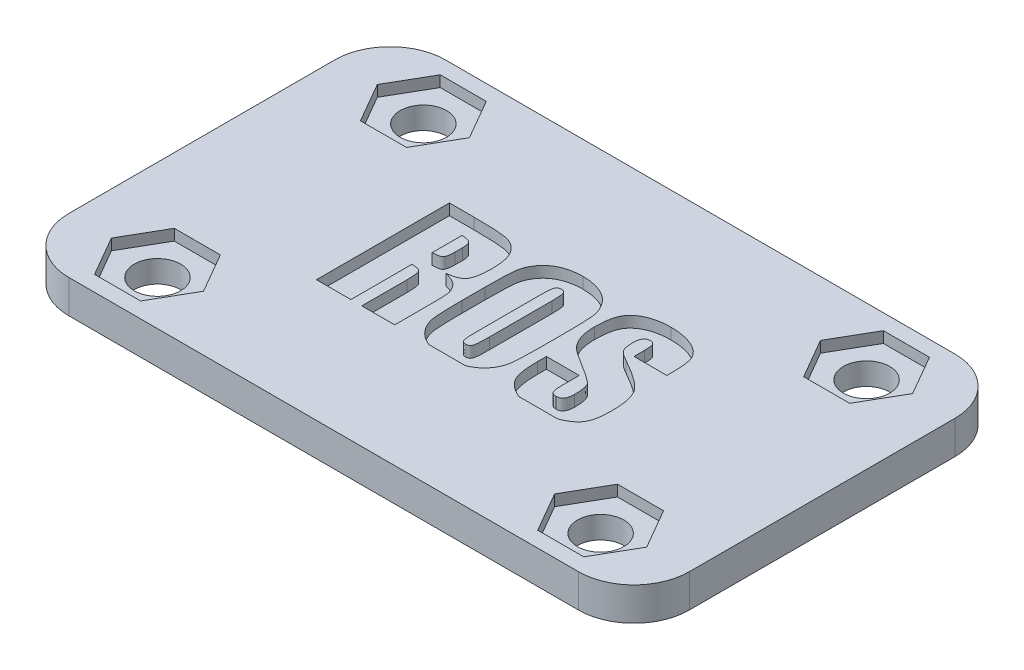
SolidWorks part; units mm, degrees
ref_plane "Front Plane" through (0, 0, 0) normal (0, 0, 1) x (1, 0, 0)
ref_plane "Top Plane" through (0, 0, 0) normal (0, 1, 0) x (1, 0, 0)
ref_plane "Right Plane" through (0, 0, 0) normal (1, 0, 0) x (0, 0, -1)
sketch "Sketch1" plane through (0, 0, 0) normal (0, 1, 0) x (1, 0, 0)
  line L1 (-28, 17) -> (28, 17)
  line L2 (-28, 17) -> (-28, -17)
  line L3 (-28, -17) -> (28, -17)
  line L4 (28, 17) -> (28, -17)
  line L5 (-28, 17) -> (28, -17) construction
  line L6 (-28, -17) -> (28, 17) construction
  point P0 (0, 0)
  dimension "D1" = 34
  dimension "D2" = 56
extrude "Boss-Extrude1" add sketch "Sketch1" along normal blind 3
sketch "Sketch2" plane through (0, 3, 0) normal (0, 1, 0) x (1, 0, 0)
  circle A0 centre (-20, 12) radius 2.09
  circle A1 centre (-20, -12) radius 2.09
  dimension "D1" = 4.18
  dimension "D2" = 24
  dimension "D3" = 12
  dimension "D4" = 20
extrude "Cut-Extrude1" cut sketch "Sketch2" against normal through all
mirror "Mirror1" about plane through (0, 0, 0) normal (1, 0, 0) of "Cut-Extrude1"
fillet "Fillet1" radius 5 4 edges at (28, 1.5, -17) (28, 1.5, 17) (-28, 1.5, 17) (-28, 1.5, -17)
sketch "Sketch3" plane through (0, 3, 0) normal (0, 1, 0) x (1, 0, 0)
  line L1 (-15.8431, 12) -> (-17.9215, 15.6)
  line L2 (-17.9215, 15.6) -> (-22.0785, 15.6)
  line L3 (-22.0785, 15.6) -> (-24.1569, 12)
  line L4 (-24.1569, 12) -> (-22.0785, 8.4)
  line L5 (-22.0785, 8.4) -> (-17.9215, 8.4)
  line L6 (-17.9215, 8.4) -> (-15.8431, 12)
  line L7 (24.1569, 12) -> (22.0785, 15.6)
  line L8 (22.0785, 15.6) -> (17.9215, 15.6)
  line L9 (17.9215, 15.6) -> (15.8431, 12)
  line L10 (15.8431, 12) -> (17.9215, 8.4)
  line L11 (17.9215, 8.4) -> (22.0785, 8.4)
  line L12 (22.0785, 8.4) -> (24.1569, 12)
  line L13 (-23, -17) -> (23, -17) construction
  circle A0 centre (-20, 12) radius 3.6 construction
  circle A1 centre (20, 12) radius 3.6 construction
  circle A2 centre (-20, 12) radius 2.09 construction
  circle A3 centre (20, 12) radius 2.09 construction
  dimension "D1" = 7.2
extrude "Cut-Extrude2" cut sketch "Sketch3" against normal blind 1
mirror "Mirror2" about plane through (0, 0, 0) normal (0, 0, 1) of "Cut-Extrude2"
sketch "Sketch4" plane through (0, 3, 0) normal (0, 1, 0) x (1, 0, 0)
  line L0 (-17, -6) -> (17, -6)
  line L1 (-11.6471, 6) -> (-9.4103, 6)
  line L2 (-4.5882, -2.7949) -> (-4.5882, -6)
  line L3 (-4.5882, -6) -> (-7.5529, -6)
  line L4 (-7.5529, -6) -> (-7.5529, -1.9412)
  line L5 (-8.5412, -0.4941) -> (-8.5412, -6)
  line L6 (-8.5412, -6) -> (-11.6471, -6)
  line L7 (-11.6471, -6) -> (-11.6471, 6)
  line L8 (-8.5412, 4.0235) -> (-8.5412, 1.3412)
  line L9 (-7.5529, 2.4287) -> (-7.5529, 3.0926)
  line L10 (-3.4588, -1.0324) -> (-3.4588, 1.0324)
  line L11 (3.7412, 1.0324) -> (3.7412, -1.0324)
  line L12 (-0.3529, 2.9757) -> (-0.3529, -2.7397)
  line L13 (0.6353, -2.6493) -> (0.6353, 2.9757)
  line L14 (11.6471, 2.3294) -> (8.6824, 2.3294)
  line L15 (8.6824, 2.3294) -> (8.6824, 3.2779)
  line L16 (4.7294, -2.4287) -> (4.7294, -1.6235)
  line L17 (4.7294, -1.6235) -> (7.6941, -1.6235)
  line L18 (7.6941, -1.6235) -> (7.6941, -3.1787)
  line L19 (11.6471, 2.8125) -> (11.6471, 2.3294)
  spline S0 degree 3 poles (-9.4103, 6) (-9.0669, 6.0012) (-8.5749, 5.9955) (-7.9492, 5.9771) (-7.5475, 5.9606) (-7.1909, 5.9363) (-6.8797, 5.9081) (-6.6138, 5.8763) (-6.3865, 5.8368) (-6.1862, 5.7853) (-6.0014, 5.7178) (-5.8245, 5.6374) (-5.6576, 5.5369) (-5.502, 5.419) (-5.352, 5.2894) (-5.2155, 5.1388) (-5.0841, 4.9743) (-4.9654, 4.7866) (-4.865, 4.5736) (-4.7788, 4.3358) (-4.7089, 4.0722) (-4.6548, 3.7831) (-4.5993, 3.3474) (-4.5915, 3.0059) (-4.5882, 2.7706) knots 0 0 0 0 0.148881 0.213303 0.271377 0.323138 0.368276 0.406827 0.439217 0.468212 0.496346 0.524443 0.552325 0.580569 0.609028 0.638128 0.668547 0.700209 0.734143 0.770448 0.80973 0.852244 0.897872 1 1 1 1
  spline S1 degree 3 poles (-4.5882, 2.7706) (-4.5847, 2.5592) (-4.5991, 2.256) (-4.6321, 1.8709) (-4.6732, 1.6245) (-4.7199, 1.4058) (-4.7787, 1.2138) (-4.8506, 1.0509) (-4.9341, 0.9125) (-5.0352, 0.7962) (-5.1554, 0.6939) (-5.2985, 0.6065) (-5.4611, 0.5289) (-5.6443, 0.4631) (-5.9295, 0.3905) (-6.1567, 0.3569) (-6.3154, 0.3441) knots 0 0 0 0 0.18379 0.264137 0.336087 0.400976 0.458649 0.510492 0.555595 0.598692 0.64408 0.692369 0.744168 0.800637 0.861472 1 1 1 1
  spline S2 degree 3 poles (-6.3154, 0.3441) (-6.1721, 0.3049) (-5.9643, 0.2494) (-5.706, 0.1522) (-5.5411, 0.0744) (-5.3931, -0.0045) (-5.2653, -0.0902) (-5.1556, -0.181) (-5.0387, -0.3053) (-4.9212, -0.4619) (-4.8041, -0.6448) (-4.7194, -0.8218) (-4.6697, -0.9719) (-4.6478, -1.1078) (-4.6293, -1.2429) (-4.6181, -1.4146) (-4.6068, -1.622) (-4.5986, -1.8647) (-4.5883, -2.2595) (-4.5915, -2.5736) (-4.5882, -2.7949) knots 0 0 0 0 0.11023 0.159227 0.204341 0.24532 0.283418 0.318243 0.350629 0.40972 0.463107 0.511383 0.554826 0.57974 0.613275 0.655917 0.707227 0.767226 0.835926 1 1 1 1
  spline S3 degree 3 poles (-7.5529, -1.9412) (-7.5542, -1.7934) (-7.554, -1.5834) (-7.5737, -1.3189) (-7.5901, -1.1553) (-7.6124, -1.0148) (-7.6369, -0.8974) (-7.67, -0.8034) (-7.7079, -0.7287) (-7.7573, -0.6684) (-7.8245, -0.6234) (-7.9036, -0.5807) (-8.0005, -0.548) (-8.1132, -0.5251) (-8.2947, -0.5004) (-8.4396, -0.4949) (-8.5412, -0.4941) knots 0 0 0 0 0.208712 0.296135 0.374434 0.440653 0.497065 0.543362 0.580978 0.614872 0.652041 0.694298 0.741574 0.795735 0.856514 1 1 1 1
  spline S4 degree 3 poles (-8.5412, 1.3412) (-8.3851, 1.3403) (-8.1682, 1.3525) (-7.9124, 1.4151) (-7.791, 1.4674) (-7.718, 1.5343) (-7.6711, 1.6021) (-7.6355, 1.6922) (-7.6049, 1.8009) (-7.5815, 1.9295) (-7.5561, 2.1403) (-7.5563, 2.3097) (-7.5529, 2.4287) knots 0 0 0 0 0.26319 0.361521 0.442778 0.481273 0.526535 0.580255 0.643242 0.716208 0.799609 1 1 1 1
  spline S5 degree 3 poles (-7.5529, 3.0926) (-7.5545, 3.251) (-7.5655, 3.4729) (-7.66, 3.7254) (-7.7586, 3.8532) (-7.9007, 3.9314) (-8.1584, 4.0148) (-8.3828, 4.0205) (-8.5412, 4.0235) knots 0 0 0 0 0.296724 0.405999 0.497474 0.590179 0.702697 1 1 1 1
  spline S6 degree 3 poles (3.7412, -1.0324) (3.7385, -1.3125) (3.74, -1.7169) (3.7317, -2.2339) (3.7191, -2.5721) (3.71, -2.8766) (3.6939, -3.1487) (3.6767, -3.3877) (3.6517, -3.661) (3.6003, -3.9749) (3.4883, -4.3317) (3.3296, -4.6711) (3.1303, -4.9928) (2.887, -5.2876) (2.6016, -5.5477) (2.2768, -5.7719) (1.913, -5.9572) (1.5147, -6.1011) (0.926, -6.2488) (0.4589, -6.2785) (0.1412, -6.2824) knots 0 0 0 0 0.112809 0.162854 0.208179 0.249065 0.285542 0.317902 0.345566 0.396043 0.445676 0.495616 0.546553 0.597656 0.649001 0.701564 0.75612 0.812885 0.871769 1 1 1 1
  spline S7 degree 3 poles (0.1412, -6.2824) (-0.1648, -6.2831) (-0.6144, -6.2452) (-1.1897, -6.1149) (-1.5848, -5.9757) (-1.9508, -5.7992) (-2.2779, -5.5765) (-2.5736, -5.321) (-2.8223, -5.0216) (-3.0318, -4.6996) (-3.1943, -4.3589) (-3.3103, -4.0053) (-3.368, -3.6952) (-3.392, -3.4245) (-3.4096, -3.1854) (-3.4246, -2.9111) (-3.4383, -2.603) (-3.4461, -2.2596) (-3.4555, -1.7324) (-3.458, -1.3191) (-3.4588, -1.0324) knots 0 0 0 0 0.123179 0.180929 0.237119 0.291548 0.344027 0.396062 0.448383 0.50021 0.550408 0.599943 0.649656 0.677029 0.709392 0.746168 0.787661 0.833574 0.884513 1 1 1 1
  spline S8 degree 3 poles (-3.4588, 1.0324) (-3.4561, 1.3132) (-3.4578, 1.7177) (-3.4492, 2.2346) (-3.437, 2.5721) (-3.4266, 2.8773) (-3.4146, 3.1495) (-3.3962, 3.3884) (-3.3721, 3.6612) (-3.3171, 3.9747) (-3.206, 4.3317) (-3.0479, 4.6709) (-2.8464, 4.9909) (-2.6056, 5.2885) (-2.3171, 5.546) (-1.9944, 5.773) (-1.63, 5.9562) (-1.2327, 6.1053) (-0.6417, 6.2443) (-0.1769, 6.2856) (0.1412, 6.2824) knots 0 0 0 0 0.1131 0.162847 0.20817 0.249054 0.28581 0.317873 0.345536 0.396062 0.445693 0.495631 0.546315 0.597643 0.649205 0.701523 0.756077 0.812942 0.872041 1 1 1 1
  spline S9 degree 3 poles (0.1412, 6.2824) (0.4469, 6.2818) (0.8967, 6.2477) (1.4702, 6.1117) (1.8645, 5.9733) (2.2316, 5.7988) (2.5599, 5.5778) (2.8536, 5.3201) (3.1028, 5.0218) (3.3114, 4.6989) (3.4772, 4.3595) (3.5927, 4.0046) (3.6506, 3.6938) (3.6735, 3.4229) (3.6959, 3.1849) (3.7057, 2.911) (3.7213, 2.6031) (3.7275, 2.2595) (3.7434, 1.7325) (3.7366, 1.3191) (3.7412, 1.0324) knots 0 0 0 0 0.123202 0.180743 0.236944 0.291253 0.343988 0.395811 0.448142 0.499979 0.550314 0.59986 0.649873 0.677251 0.709348 0.746116 0.787617 0.833538 0.884493 1 1 1 1
  spline S10 degree 3 poles (0.6353, 2.9757) (0.6349, 3.1052) (0.6314, 3.2898) (0.6236, 3.523) (0.6121, 3.6693) (0.5991, 3.7965) (0.585, 3.9051) (0.5651, 3.9935) (0.5377, 4.0836) (0.4873, 4.1724) (0.3682, 4.2858) (0.2378, 4.3035) (0.1566, 4.3059) knots 0 0 0 0 0.245382 0.350014 0.44228 0.523563 0.592561 0.649714 0.69512 0.770679 0.840726 1 1 1 1
  spline S11 degree 3 poles (0.1566, 4.3059) (0.0809, 4.3097) (-0.0301, 4.2831) (-0.155, 4.2004) (-0.2173, 4.1263) (-0.2587, 4.0467) (-0.283, 3.962) (-0.3051, 3.8552) (-0.3211, 3.7245) (-0.3378, 3.5709) (-0.3473, 3.3184) (-0.3544, 3.1178) (-0.3529, 2.9757) knots 0 0 0 0 0.141273 0.207934 0.278501 0.320511 0.375555 0.443281 0.525523 0.622695 0.733336 1 1 1 1
  spline S12 degree 3 poles (-0.3529, -2.7397) (-0.3502, -2.9007) (-0.3519, -3.1295) (-0.3437, -3.4171) (-0.331, -3.5941) (-0.3222, -3.7459) (-0.3063, -3.8724) (-0.2896, -3.9735) (-0.2657, -4.0719) (-0.2162, -4.1673) (-0.0898, -4.2859) (0.0478, -4.3054) (0.1346, -4.3059) knots 0 0 0 0 0.263966 0.37491 0.47152 0.554902 0.624119 0.680394 0.722784 0.789642 0.853612 1 1 1 1
  spline S13 degree 3 poles (0.1346, -4.3059) (0.2255, -4.3075) (0.3671, -4.2777) (0.4949, -4.1446) (0.5422, -4.0365) (0.5704, -3.9275) (0.586, -3.8179) (0.6017, -3.6841) (0.615, -3.5252) (0.6226, -3.3412) (0.6323, -3.0464) (0.6344, -2.8132) (0.6353, -2.6493) knots 0 0 0 0 0.145036 0.209347 0.281953 0.327187 0.385478 0.455017 0.538188 0.634996 0.743262 1 1 1 1
  spline S14 degree 3 poles (8.6824, 3.2779) (8.6818, 3.4588) (8.6776, 3.7029) (8.6263, 3.9859) (8.5738, 4.1183) (8.4978, 4.207) (8.3666, 4.2877) (8.2475, 4.3082) (8.1662, 4.3059) knots 0 0 0 0 0.412843 0.553103 0.65361 0.73318 0.814494 1 1 1 1
  spline S15 degree 3 poles (8.1662, 4.3059) (8.076, 4.3052) (7.9379, 4.2803) (7.7902, 4.1738) (7.6998, 4.0667) (7.6311, 3.9284) (7.5692, 3.6856) (7.549, 3.4865) (7.5529, 3.3441) knots 0 0 0 0 0.212113 0.312859 0.418563 0.535756 0.66915 1 1 1 1
  spline S16 degree 3 poles (7.5529, 3.3441) (7.5516, 3.1611) (7.5694, 2.8413) (7.6434, 2.5283) (7.7029, 2.4044) knots 0 0 0 0 0.572651 1 1 1 1
  spline S17 degree 3 poles (7.7029, 2.4044) (7.7322, 2.3452) (7.7942, 2.2581) (7.8995, 2.147) (8.0059, 2.059) (8.1288, 1.9644) (8.3296, 1.8295) (8.496, 1.7357) (8.6118, 1.6699) knots 0 0 0 0 0.166753 0.269572 0.387216 0.516182 0.662459 1 1 1 1
  spline S18 degree 3 poles (8.6118, 1.6699) (8.9472, 1.484) (9.4257, 1.211) (10.0156, 0.8328) (10.3851, 0.5738) (10.7061, 0.3313) (11.0411, 0.0406) (11.2578, -0.1815) (11.3669, -0.3397) knots 0 0 0 0 0.335278 0.4813 0.612364 0.729739 0.832713 1 1 1 1
  spline S19 degree 3 poles (11.3669, -0.3397) (11.4674, -0.4836) (11.5941, -0.7269) (11.7151, -1.0863) (11.7938, -1.3946) (11.8552, -1.7344) (11.9148, -2.2468) (11.9294, -2.6482) (11.9294, -2.925) knots 0 0 0 0 0.195997 0.304678 0.423526 0.551406 0.690506 1 1 1 1
  spline S20 degree 3 poles (11.9294, -2.925) (11.9306, -3.1274) (11.921, -3.4206) (11.8877, -3.7962) (11.8559, -4.046) (11.8113, -4.2742) (11.7592, -4.4814) (11.6979, -4.6686) (11.6247, -4.8366) (11.5365, -4.9904) (11.4313, -5.1345) (11.31, -5.2737) (11.1701, -5.4062) (11.0125, -5.5328) (10.8359, -5.6506) (10.6422, -5.7639) (10.3591, -5.9089) (9.9729, -6.059) (9.2933, -6.2392) (8.7537, -6.28) (8.3868, -6.2824) knots 0 0 0 0 0.107307 0.155459 0.199907 0.240819 0.278648 0.313174 0.345124 0.37569 0.406967 0.439576 0.4735 0.509002 0.546638 0.58596 0.627987 0.715167 0.805112 1 1 1 1
  spline S21 degree 3 poles (8.3868, -6.2824) (8.1804, -6.2854) (7.8765, -6.2668) (7.481, -6.2177) (7.2012, -6.1639) (6.9326, -6.0967) (6.6761, -6.0115) (6.43, -5.9163) (6.1998, -5.8006) (5.9838, -5.6755) (5.7857, -5.5421) (5.6073, -5.3994) (5.4478, -5.2498) (5.3077, -5.0905) (5.1891, -4.9216) (5.0852, -4.7476) (5.0057, -4.5597) (4.9402, -4.3592) (4.8815, -4.1416) (4.8378, -3.9036) (4.7968, -3.6464) (4.767, -3.3696) (4.7367, -2.9616) (4.7296, -2.6457) (4.7294, -2.4287) knots 0 0 0 0 0.100145 0.147666 0.193464 0.238409 0.281993 0.324627 0.366464 0.406944 0.445764 0.482345 0.517706 0.551866 0.585155 0.617796 0.650099 0.683973 0.720175 0.759459 0.801374 0.84664 0.894618 1 1 1 1
  spline S22 degree 3 poles (7.6941, -3.1787) (7.6926, -3.2877) (7.7, -3.4427) (7.7093, -3.6394) (7.7266, -3.7627) (7.7414, -3.871) (7.7672, -3.9619) (7.7922, -4.038) (7.8328, -4.1177) (7.9024, -4.1962) (8.0568, -4.2904) (8.2004, -4.3038) (8.2963, -4.3059) knots 0 0 0 0 0.221449 0.31586 0.400263 0.474516 0.538003 0.591926 0.637412 0.719013 0.801608 1 1 1 1
  spline S23 degree 3 poles (8.2963, -4.3059) (8.3981, -4.3086) (8.5473, -4.2778) (8.713, -4.1688) (8.8065, -4.053) (8.8803, -3.9083) (8.9485, -3.6569) (8.9647, -3.4501) (8.9647, -3.3044) knots 0 0 0 0 0.223296 0.324627 0.430189 0.546596 0.679609 1 1 1 1
  spline S24 degree 3 poles (8.9647, -3.3044) (8.9649, -3.1381) (8.9574, -2.9001) (8.9286, -2.5983) (8.8949, -2.4078) (8.857, -2.2394) (8.7927, -2.0592) (8.7313, -1.9386) (8.6757, -1.875) knots 0 0 0 0 0.336674 0.481824 0.613234 0.728042 0.830673 1 1 1 1
  spline S25 degree 3 poles (8.6757, -1.875) (8.6126, -1.8041) (8.4954, -1.699) (8.3122, -1.5594) (8.137, -1.4289) (7.9303, -1.2881) (7.5985, -1.0708) (7.3298, -0.9089) (7.1426, -0.7941) knots 0 0 0 0 0.151175 0.250667 0.367276 0.49971 0.649705 1 1 1 1
  spline S26 degree 3 poles (7.1426, -0.7941) (6.9527, -0.6788) (6.6813, -0.5122) (6.34, -0.2922) (6.1235, -0.1475) (5.9316, -0.0168) (5.767, 0.1018) (5.6269, 0.2072) (5.4751, 0.3341) (5.311, 0.5032) (5.1361, 0.7318) (4.9799, 0.9943) (4.8394, 1.2899) (4.7229, 1.6247) (4.6172, 2.1551) (4.5843, 2.5772) (4.5882, 2.8721) knots 0 0 0 0 0.139497 0.199929 0.25485 0.30299 0.345648 0.382207 0.412998 0.469794 0.529711 0.593278 0.661207 0.734924 0.815133 1 1 1 1
  spline S27 degree 3 poles (4.5882, 2.8721) (4.5915, 3.089) (4.5956, 3.4033) (4.6361, 3.8052) (4.6748, 4.0719) (4.7257, 4.3157) (4.7856, 4.5371) (4.8612, 4.7336) (4.9459, 4.9098) (5.0448, 5.0692) (5.1582, 5.2159) (5.2818, 5.3578) (5.4237, 5.4859) (5.5773, 5.6088) (5.7441, 5.7233) (5.9262, 5.8266) (6.1895, 5.9555) (6.5504, 6.088) (7.1983, 6.2468) (7.715, 6.2821) (8.0691, 6.2824) knots 0 0 0 0 0.115094 0.16642 0.214115 0.25793 0.298418 0.335563 0.369391 0.401957 0.434786 0.46765 0.501588 0.535991 0.571894 0.608743 0.64693 0.727243 0.81197 1 1 1 1
  spline S28 degree 3 poles (8.0691, 6.2824) (8.2698, 6.2794) (8.5663, 6.2747) (8.9506, 6.2262) (9.223, 6.1872) (9.4831, 6.128) (9.7326, 6.0611) (9.9699, 5.979) (10.194, 5.8841) (10.4035, 5.7811) (10.5978, 5.6745) (10.7692, 5.555) (10.9282, 5.4368) (11.0618, 5.3035) (11.1838, 5.1702) (11.2823, 5.0262) (11.3651, 4.8734) (11.4309, 4.703) (11.491, 4.5119) (11.5377, 4.2929) (11.5805, 4.0489) (11.6097, 3.7769) (11.6403, 3.3624) (11.6468, 3.0376) (11.6471, 2.8125) knots 0 0 0 0 0.103081 0.151694 0.198641 0.244219 0.288419 0.331125 0.37288 0.413199 0.450863 0.486435 0.520313 0.552325 0.583055 0.612876 0.641566 0.672036 0.706398 0.744284 0.786764 0.83346 0.884523 1 1 1 1
  point P2 (0, -6)
  dimension "D1" = 34
  dimension "D2" = 6
extrude "Cut-Extrude3" cut sketch "Sketch4" against normal blind 1 contours S3 L4 L0 L2 S2 S1 S0 L1 L7 L5 S5 L9 S4 L8 | S9 S8 L10 S7 L0 S6 L11 S13 S12 L12 S11 S10 L13 | S28 S27 S26 S25 S24 S23 S22 L18 L17 L16 S21 L0 S20 S19 S18 S17 S16 S15 S14 L15 L14 L19
